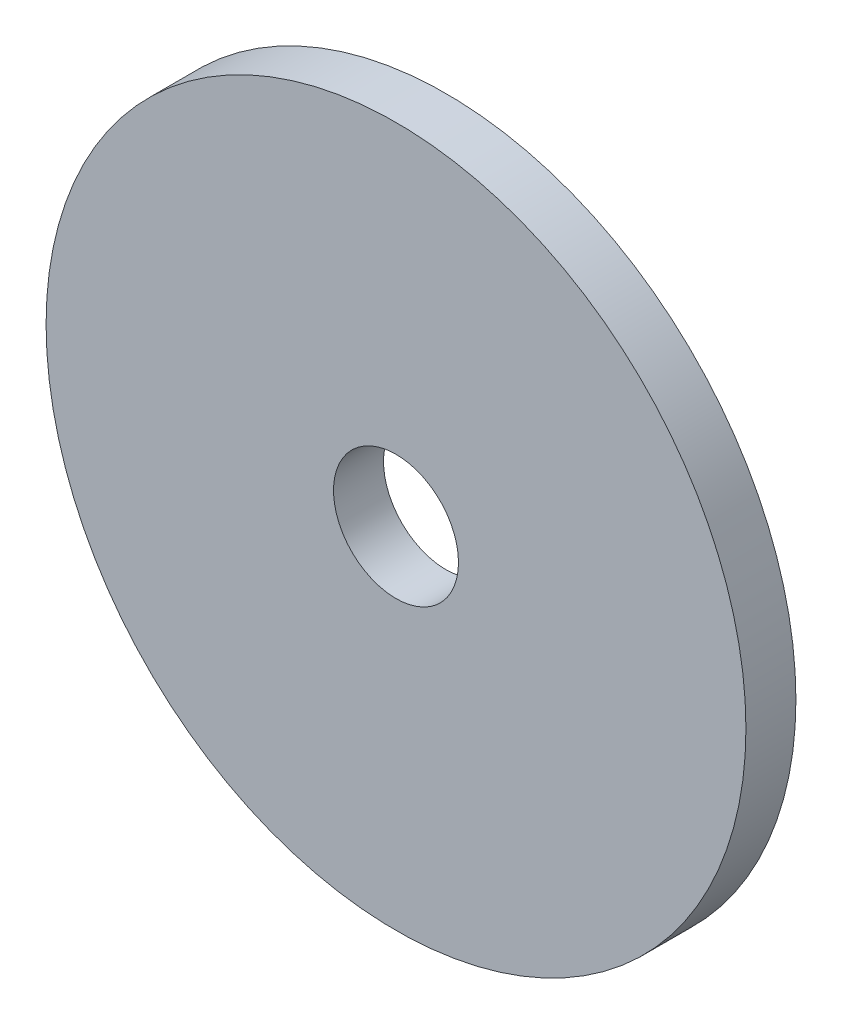
SolidWorks part; units mm, degrees
ref_plane "Front Plane" through (0, 0, 0) normal (0, 0, 1) x (1, 0, 0)
ref_plane "Top Plane" through (0, 0, 0) normal (0, 1, 0) x (1, 0, 0)
ref_plane "Right Plane" through (0, 0, 0) normal (1, 0, 0) x (0, 0, -1)
sketch "Sketch1" plane through (0, 0, 0) normal (0, 0, 1) x (1, 0, 0)
  circle A0 centre (0, 0) radius 14
  circle A1 centre (0, 0) radius 2.5
extrude "Boss-Extrude1" add sketch "Sketch1" along normal blind 2
sketch "Sketch3" plane through (0, 0, 0) normal (0, 1, 0) x (1, 0, 0)
  line L1 (0, 7.5244) -> (0, -11.2513) construction
